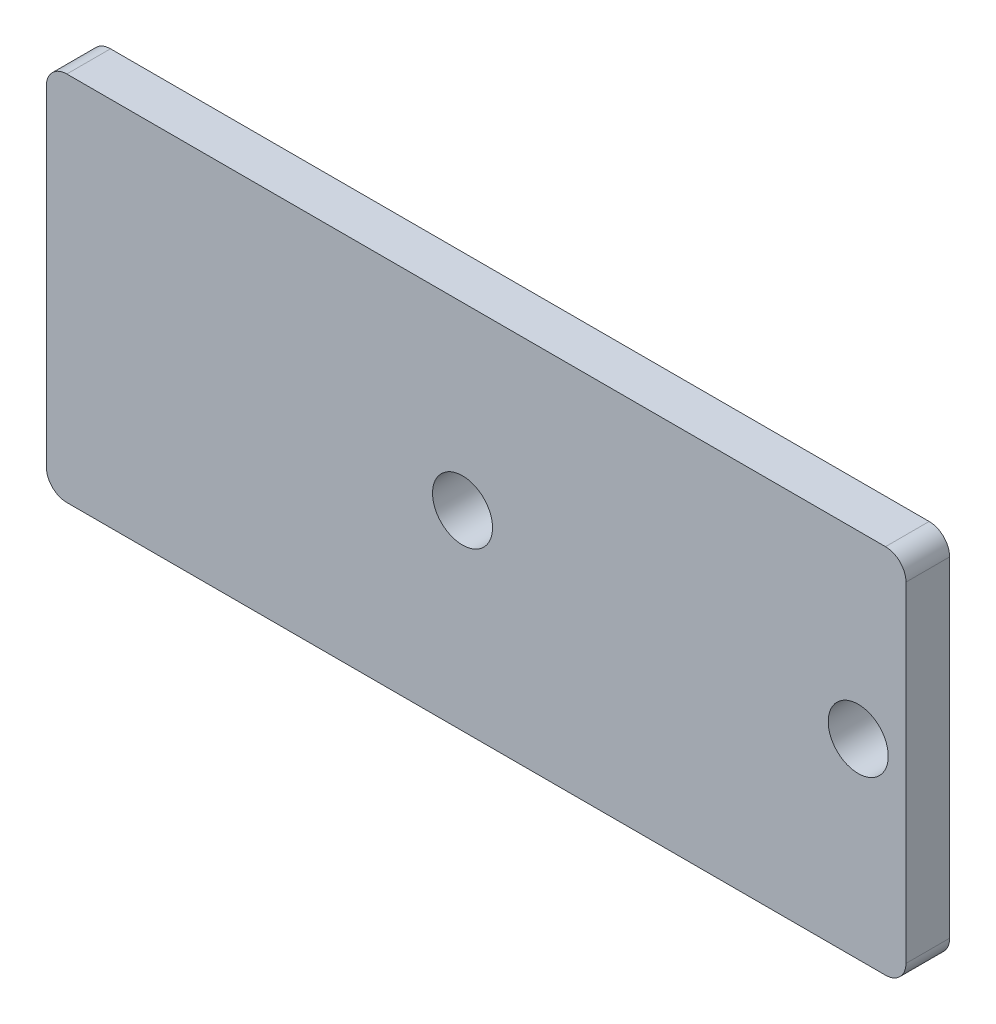
SolidWorks part; units mm, degrees
material "FR4_stuffedProtoboard"
ref_plane "Front Plane" through (0, 0, 0) normal (0, 0, 1) x (1, 0, 0)
ref_plane "Top Plane" through (0, 0, 0) normal (0, 1, 0) x (1, 0, 0)
ref_plane "Right Plane" through (0, 0, 0) normal (1, 0, 0) x (0, 0, -1)
sketch "Model" plane through (0, 0, 0) normal (0, 0, 1) x (1, 0, 0)
  line L0 (-15, -6.8) -> (15, -6.8)
  line L1 (15.75, -6.05) -> (15.75, 6.05)
  line L2 (-15, 6.8) -> (15, 6.8)
  line L3 (-15.75, 6.05) -> (-15.75, -6.05)
  arc A0 (-15, 6.8) -> (-15.75, 6.05) centre (-15, 6.05) ccw
  arc A1 (15, 6.8) -> (15.75, 6.05) centre (15, 6.05) cw
  arc A2 (15, -6.8) -> (15.75, -6.05) centre (15, -6.05) ccw
  arc A3 (-15, -6.8) -> (-15.75, -6.05) centre (-15, -6.05) cw
  circle A4 centre (-0.5, 0.2) radius 1.1
  circle A5 centre (14, 0.2) radius 1.1
  point P2 (0, -6.8)
  point P7 (-15.75, 6.8)
  point P17 (15.75, -6.8)
  point P20 (-15.75, -6.8)
  point P24 (15.75, 0)
  dimension "D3" = 7
  dimension "D7" = 31.5
  dimension "D8" = 2.2
  dimension "D9" = 2.2
  dimension "D1" = 0.75
  dimension "D2" = 13.6
  dimension "D5" = 14.5
  dimension "D6" = 1.75
extrude "Boss-Extrude1" add sketch "Model" along normal mid plane 1.6
sketch "Sketch1" plane through (0, 0, 0.8) normal (0, 0, 1) x (1, 0, 0)
  line L0 (-6.35, -1.6) -> (-6.35, 2) construction
  line L1 (-13.75, 5.2) -> (-3.75, 5.2)
  line L2 (-13.75, 5.2) -> (-13.75, -4.8)
  line L3 (-13.75, -4.8) -> (-3.75, -4.8)
  line L4 (-3.75, 5.2) -> (-3.75, -4.8)
  line L5 (-15.75, 6.05) -> (-15.75, -6.05) construction
  line L6 (-6.35, 2) -> (-11.15, 2) construction
  line L7 (-15, -6.8) -> (15, -6.8) construction
  line L8 (-11.15, 2) -> (-11.15, -1.6) construction
  line L9 (-11.15, -1.6) -> (-6.35, -1.6) construction
  line L10 (-6.35, -1.6) -> (-6.35, 2)
  line L11 (-6.35, 2) -> (-11.15, 2)
  line L12 (-11.15, 2) -> (-11.15, -1.6)
  line L13 (-11.15, -1.6) -> (-6.35, -1.6)
  line L14 (-5.25, -3.3) -> (-12.25, -3.3) construction
  line L15 (-12.25, -3.3) -> (-12.25, 3.7) construction
  line L16 (-12.25, 3.7) -> (-5.25, 3.7) construction
  line L17 (-5.25, 3.7) -> (-5.25, -3.3) construction
  line L18 (-5.25, -3.3) -> (-12.25, -3.3)
  line L19 (-12.25, -3.3) -> (-12.25, 3.7)
  line L20 (-12.25, 3.7) -> (-5.25, 3.7)
  line L21 (-5.25, 3.7) -> (-5.25, -3.3)
  dimension "D1" = 2
  dimension "D2" = 2
  dimension "D3" = 10
  dimension "D4" = 10
